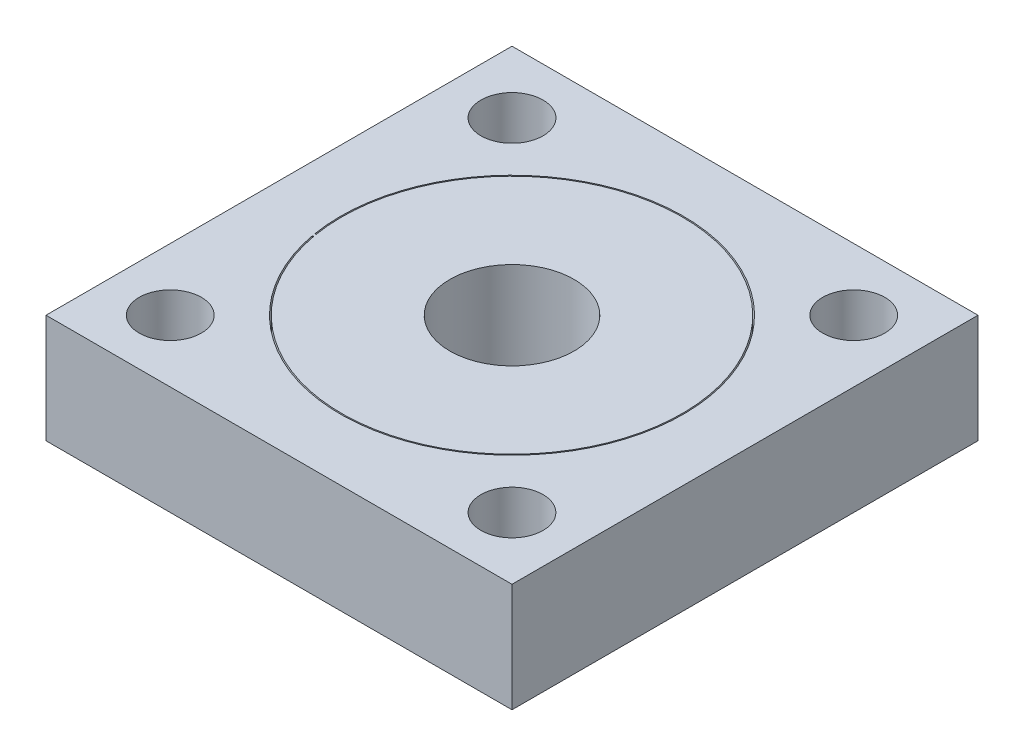
SolidWorks part; units mm, degrees
ref_plane "Front Plane" through (0, 0, 0) normal (0, 0, 1) x (1, 0, 0)
ref_plane "Top Plane" through (0, 0, 0) normal (0, 1, 0) x (1, 0, 0)
ref_plane "Right Plane" through (0, 0, 0) normal (1, 0, 0) x (0, 0, -1)
sketch "Sketch1" plane through (0, 0, 0) normal (0, 1, 0) x (1, 0, 0)
  line L1 (-15, 15) -> (15, 15)
  line L2 (-15, 15) -> (-15, -15)
  line L3 (-15, -15) -> (15, -15)
  line L4 (15, 15) -> (15, -15)
  line L5 (-15, 15) -> (15, -15) construction
  line L6 (-15, -15) -> (15, 15) construction
  circle A1 centre (0, 0) radius 4
  point P0 (0, 0)
extrude "Boss-Extrude1" add sketch "Sketch1" along normal blind 7
sketch "Sketch2" plane through (0, 0, 0) normal (0, -1, 0) x (1, 0, 0)
  arc A1 (-10.8519, 1.7989) -> (-10.8189, 1.988) centre (0, 0) ccw
extrude "Cut-Extrude-Thin1" cut sketch "Sketch2" against normal blind 10 and the other way through all thin thin type mid plane wall 0.08
sketch "Sketch3" plane through (0, 7, 0) normal (0, 1, 0) x (1, 0, 0)
  circle A0 centre (11, 11) radius 2
extrude "Cut-Extrude1" cut sketch "Sketch3" against normal blind 10
pattern_circular "CirPattern1" count 4 over 360 about axis through (0, 0, 0) along (0, 1, 0) of "Cut-Extrude1"
